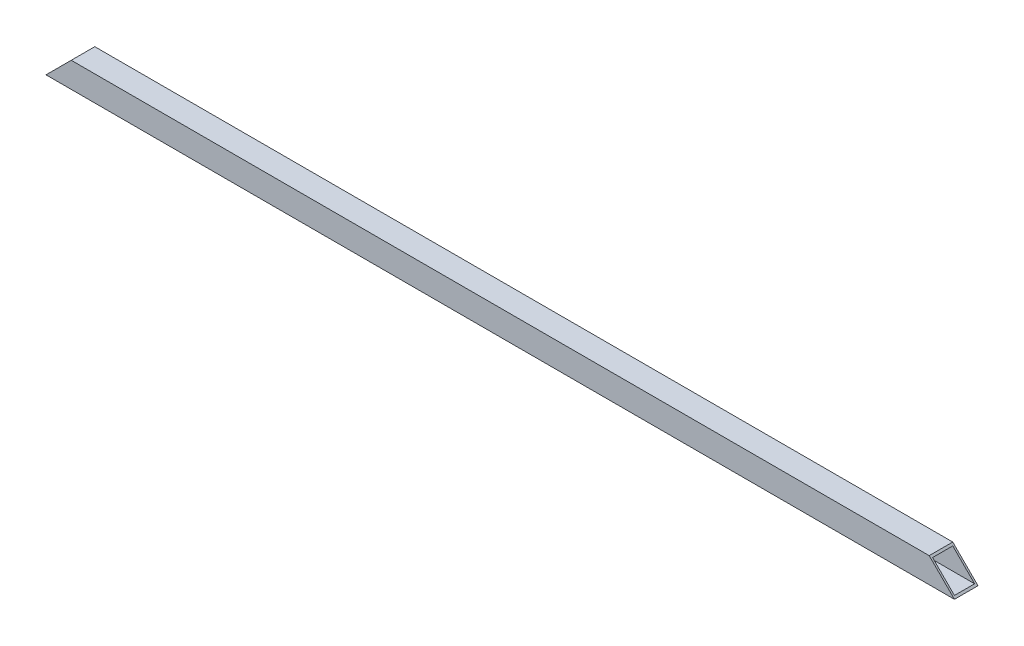
SolidWorks part; units mm, degrees
ref_plane "Спереди" through (0, 0, 0) normal (0, 0, 1) x (1, 0, 0)
ref_plane "Сверху" through (0, 0, 0) normal (0, 1, 0) x (1, 0, 0)
ref_plane "Справа" through (0, 0, 0) normal (1, 0, 0) x (0, 0, -1)
sketch "Эскиз2" plane through (0, 0, 0) normal (1, 0, 0) x (0, 0, -1)
  line L1 (-35, 37.5) -> (35, 37.5)
  line L2 (-35, 37.5) -> (-35, -37.5)
  line L3 (-35, -37.5) -> (35, -37.5)
  line L4 (35, 37.5) -> (35, -37.5)
  line L5 (-35, 37.5) -> (35, -37.5) construction
  line L6 (-35, -37.5) -> (35, 37.5) construction
  point P0 (0, 0)
extrude "Вытянуть-Тонкостенный1" add sketch "Эскиз2" along normal blind 2700 thin
sketch "Эскиз3" plane through (0, 0, -35) normal (0, 0, -1) x (-1, 0, 0)
  line L0 (-2700, -37.5) -> (-2625, 37.5)
  line L1 (-2700, 37.5) -> (0, 37.5) construction
  line L2 (-2625, 37.5) -> (-75, 37.5)
  line L3 (-75, 37.5) -> (0, -37.5)
  line L4 (0, -37.5) -> (-2700, -37.5)
extrude "Вырез-Вытянуть1" cut sketch "Эскиз3" against normal through all flip side to cut
